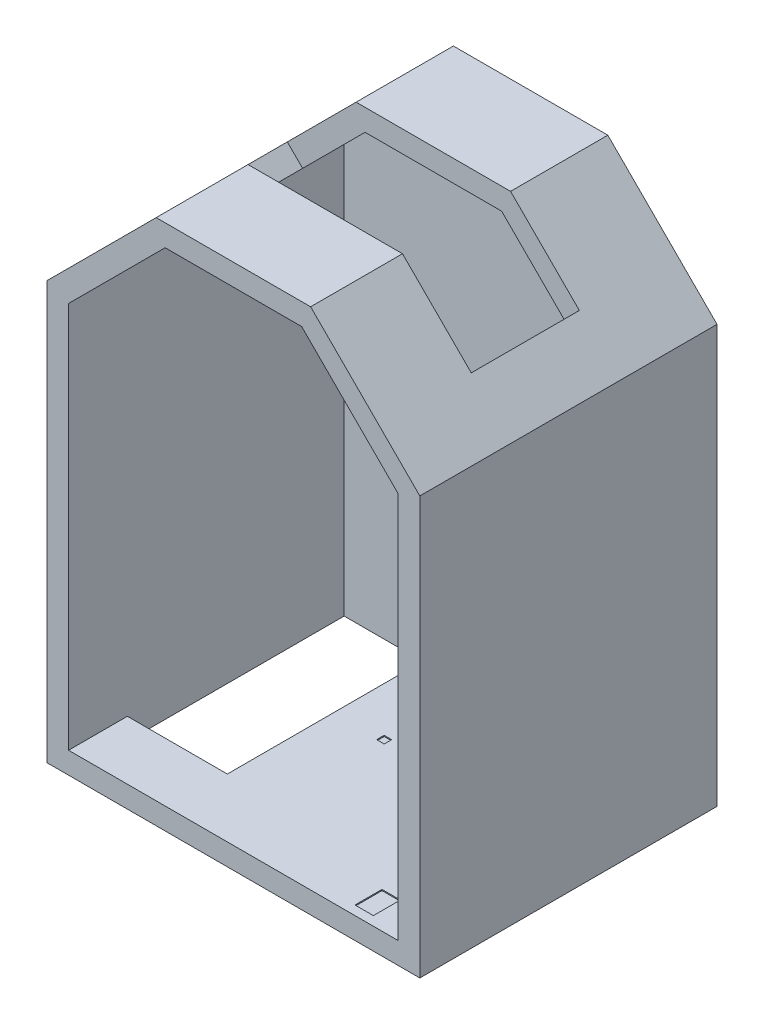
SolidWorks part; units mm, degrees
ref_plane "Front Plane" through (0, 0, 0) normal (0, 0, 1) x (1, 0, 0)
ref_plane "Top Plane" through (0, 0, 0) normal (0, 1, 0) x (1, 0, 0)
ref_plane "Right Plane" through (0, 0, 0) normal (1, 0, 0) x (0, 0, -1)
sketch "Sketch1" plane through (0, 0, 0) normal (0, 0, 1) x (1, 0, 0)
  line L0 (959.3738, -990) -> (959.3738, 2590)
  line L1 (66.0495, 3483.3243) -> (148.8922, 3683.3243) construction
  line L2 (-1197.3018, 3483.3243) -> (66.0495, 3483.3243)
  line L4 (1159.3738, 2672.8427) -> (1159.3738, -1190)
  line L6 (-1197.3018, 3483.3243) -> (-1280.1446, 3683.3243)
  line L22 (959.3738, -990) -> (-1165.6262, -990)
  line L23 (-1165.6262, -990) -> (-1165.6262, -1190)
  line L25 (66.0495, 3483.3243) -> (959.3738, 2590)
  line L31 (-1165.6262, -1190) -> (1159.3738, -1190)
  line L53 (1159.3738, 2672.8427) -> (148.8922, 3683.3243)
  line L54 (148.8922, 3683.3243) -> (-1280.1446, 3683.3243)
  dimension "D1" = 112.5
  dimension "D2" = 135
  dimension "D4" = 3580
  dimension "D5" = 2125
  dimension "D6" = 112.5
  dimension "D31" = 200
  dimension "D32" = 200
  dimension "D35" = 200
extrude "Base" add sketch "Sketch1" along normal blind 2550 contours L2 L25 L0 L22 L23 L31 L4 L53 L54 L6
sketch "Sketch5" plane through (0, 0, 0) normal (0, 0, 1) x (1, 0, 0)
  line L4 (1159.3738, 2672.8427) -> (1159.3738, -1190)
  line L5 (-2290.6262, -1190) -> (-2290.6262, 2672.8427)
  line L10 (-2290.6262, -1190) -> (1159.3738, -1190)
  line L11 (1159.3738, 2672.8427) -> (148.8922, 3683.3243)
  line L12 (148.8922, 3683.3243) -> (-1280.1446, 3683.3243)
  line L13 (-1280.1446, 3683.3243) -> (-2290.6262, 2672.8427)
extrude "Floor" add sketch "Sketch5" against normal blind 200
sketch "Sketch13" plane through (1916.1083, 1916.1083, 0) normal (0.7071, 0.7071, 0) x (0, 0, -1)
  line L0 (-2550, 2499.2209) -> (200, 2499.2209) construction
  line L1 (-1700, 2499.2209) -> (-700, 2499.2209)
  line L2 (-1700, 2499.2209) -> (-1700, 1599.2209)
  line L3 (-1700, 1599.2209) -> (-700, 1599.2209)
  line L4 (-700, 2499.2209) -> (-700, 1599.2209)
  line L5 (200, 1070.1841) -> (200, 2499.2209) construction
  dimension "D1" = 900
  dimension "D2" = 1000
  dimension "D3" = 900
extrude "Window right" cut sketch "Sketch13" against normal through all
sketch "Sketch14" plane through (0, 3683.3243, 0) normal (0, 1, 0) x (1, 0, 0)
  line L0 (-1280.1446, -2550) -> (-1280.1446, 0) construction
  line L1 (148.8922, -1700) -> (-1280.1446, -1700)
  line L2 (148.8922, -1700) -> (148.8922, -700)
  line L3 (148.8922, -700) -> (-1280.1446, -700)
  line L4 (-1280.1446, -1700) -> (-1280.1446, -700)
  line L5 (785.2883, -700) -> (148.8922, -700) construction
extrude "Window center" cut sketch "Sketch14" against normal blind 500
sketch "Sketch8" plane through (0, -990, 0) normal (0, 1, 0) x (1, 0, 0)
  line L0 (959.3738, -2550) -> (-1165.6262, -2550) construction
  line L1 (474.3738, -2215) -> (644.3738, -2215)
  line L2 (474.3738, -2215) -> (474.3738, -2465)
  line L3 (474.3738, -2465) -> (644.3738, -2465)
  line L4 (644.3738, -2215) -> (644.3738, -2465)
  line L5 (474.3738, -2215) -> (644.3738, -2465) construction
  line L6 (474.3738, -2465) -> (644.3738, -2215) construction
  line L7 (959.3738, -2550) -> (959.3738, 0) construction
  point P0 (559.3738, -2340)
  dimension "D1" = 210
  dimension "D2" = 400
  dimension "D3" = 250
  dimension "D4" = 170
extrude "Ventilation" cut sketch "Sketch8" against normal blind 10
sketch "Sketch9" plane through (0, -990, 0) normal (0, 1, 0) x (1, 0, 0)
  line L0 (959.3738, -2550) -> (959.3738, 0) construction
  line L2 (959.3738, 0) -> (-1165.6262, 0) construction
  line L3 (-750.6262, -970) -> (-680.6262, -970)
  line L4 (-750.6262, -970) -> (-750.6262, -1040)
  line L5 (-750.6262, -1040) -> (-680.6262, -1040)
  line L6 (-680.6262, -970) -> (-680.6262, -1040)
  line L7 (-750.6262, -970) -> (-680.6262, -1040) construction
  line L8 (-750.6262, -1040) -> (-680.6262, -970) construction
  circle A0 centre (439.3738, -400) radius 15
  circle A1 centre (439.3738, -285) radius 15
  circle A2 centre (244.3738, -75) radius 32.5
  point P10 (-715.6262, -1005)
  dimension "D4" = 30
  dimension "D5" = 65
  dimension "D1" = 520
  dimension "D2" = 400
  dimension "D3" = 285
  dimension "D6" = 75
  dimension "D7" = 715
  dimension "D8" = 70
  dimension "D9" = 1675
  dimension "D10" = 1005
extrude "Socket & pipes" cut sketch "Sketch9" against normal blind 10
sketch "Sketch10" plane through (959.3738, 0, 0) normal (-1, 0, 0) x (0, 0, 1)
  line L0 (0, -990) -> (0, 2590) construction
  line L1 (2550, -990) -> (0, -990) construction
  line L9 (1095, 420) -> (1195, 420)
  line L10 (1095, 420) -> (1095, 320)
  line L11 (1095, 320) -> (1195, 320)
  line L12 (1195, 420) -> (1195, 320)
  line L13 (1095, 420) -> (1195, 320) construction
  line L14 (1095, 320) -> (1195, 420) construction
  line L15 (1180, 445) -> (1110, 445)
  line L16 (1180, 445) -> (1180, 585)
  line L17 (1180, 585) -> (1110, 585)
  line L18 (1110, 445) -> (1110, 585)
  line L19 (1180, 445) -> (1110, 585) construction
  line L20 (1180, 585) -> (1110, 445) construction
  point P8 (1145, 370)
  point P13 (1145, 515)
  dimension "D1" = 100
  dimension "D2" = 70
  dimension "D3" = 140
  dimension "D4" = 1145
  dimension "D5" = 1505
  dimension "D6" = 1145
  dimension "D7" = 1360
extrude "Socket" cut sketch "Sketch10" against normal blind 5
sketch "Sketch12" plane through (0, -1190, 0) normal (0, -1, 0) x (1, 0, 0)
  line L1 (-1165.6262, 2550) -> (-2237.9062, 2550)
  line L2 (-1165.6262, 2550) -> (-1165.6262, 2005.9797)
  line L3 (-1165.6262, 2005.9797) -> (-2237.9062, 2005.9797)
  line L4 (-2237.9062, 2550) -> (-2237.9062, 2005.9797)
extrude "Door high wall" add sketch "Sketch12" against normal blind 200
sketch "Sketch6" plane through (0, 0, 0) normal (0, 0, 1) x (1, 0, 0)
  line L0 (-1280.1446, 3683.3243) -> (-1197.3018, 3483.3243)
  line L1 (-2090.6262, 2590) -> (-1197.3018, 3483.3243)
  line L3 (-2090.6262, 2590) -> (-2090.6262, -1190)
  line L5 (-2290.6262, -1190) -> (-2290.6262, 2672.8427)
  line L6 (-2090.6262, -1190) -> (-2290.6262, -1190)
  line L13 (-1280.1446, 3683.3243) -> (-2290.6262, 2672.8427)
extrude "Wall" add sketch "Sketch6" along normal blind 2550
sketch "Sketch15" plane through (-2481.7344, 2481.7344, 0) normal (-0.7071, 0.7071, 0) x (0, 0, 1)
  line L1 (700, 1699.3047) -> (1700, 1699.3047)
  line L2 (700, 1699.3047) -> (700, 799.3047)
  line L3 (700, 799.3047) -> (1700, 799.3047)
  line L4 (1700, 1699.3047) -> (1700, 799.3047)
  line L5 (1700, 1699.3047) -> (1700, 2709.7863) construction
  dimension "D1" = 900
extrude "Window left" cut sketch "Sketch15" against normal blind 500
equation "\"H_CEILING\"=2550"
equation "\"D1@Wall\"=\"H_CEILING\""
equation "\"D1@Base\"=\"H_CEILING\""
